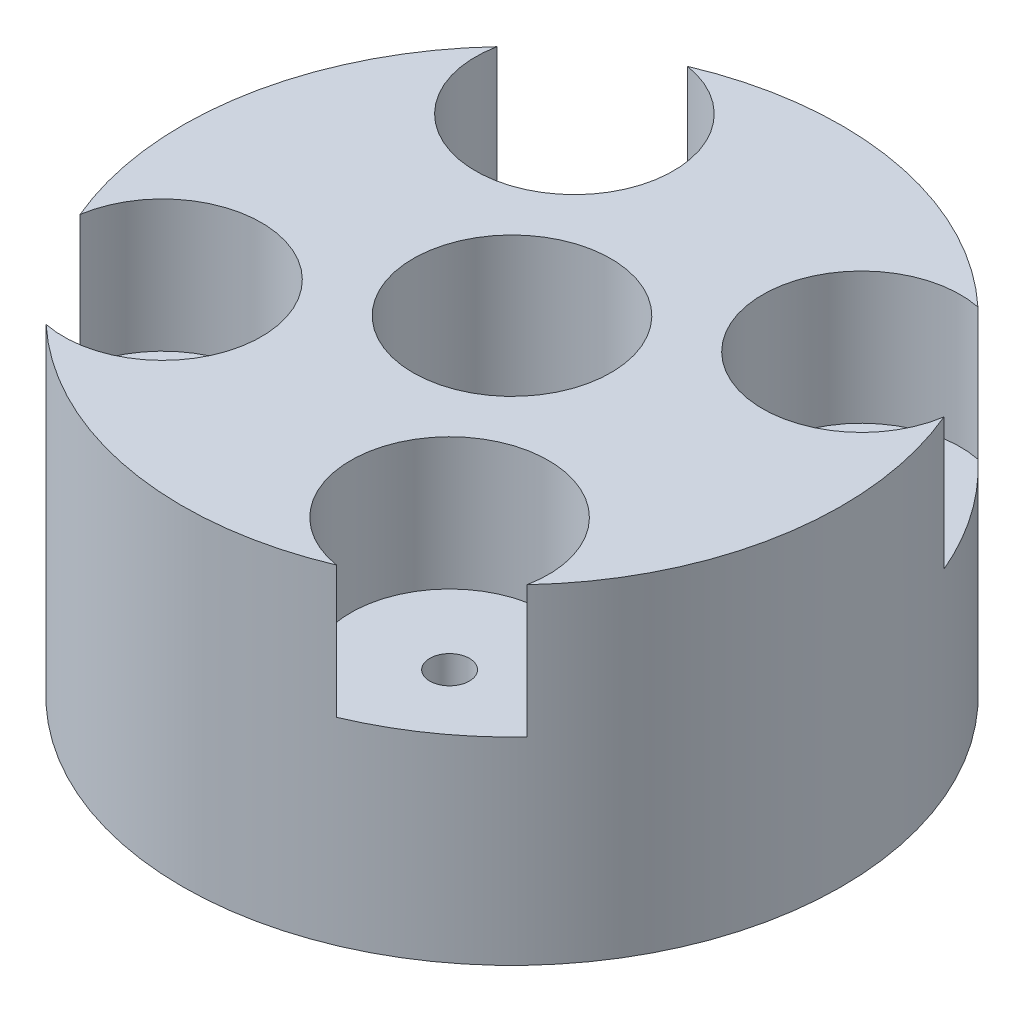
SolidWorks part; units mm, degrees
ref_plane "Alzado" through (0, 0, 0) normal (0, 0, 1) x (1, 0, 0)
ref_plane "Planta" through (0, 0, 0) normal (0, 1, 0) x (1, 0, 0)
ref_plane "Vista lateral" through (0, 0, 0) normal (1, 0, 0) x (0, 0, -1)
sketch "Croquis1" plane through (0, 0, 0) normal (0, 1, 0) x (1, 0, 0)
  circle A0 centre (0, 0) radius 10
  dimension "D1" = 20
extrude "Saliente-Extruir1" add sketch "Croquis1" along normal blind 10
sketch "Croquis2" plane through (0, 0, 0) normal (0, -1, 0) x (1, 0, 0)
  line L1 (5, 0) -> (2.5, 4.3301)
  line L2 (2.5, 4.3301) -> (-2.5, 4.3301)
  line L3 (-2.5, 4.3301) -> (-5, 0)
  line L4 (-5, 0) -> (-2.5, -4.3301)
  line L5 (-2.5, -4.3301) -> (2.5, -4.3301)
  line L6 (2.5, -4.3301) -> (5, 0)
  circle A0 centre (0, 0) radius 4.3301 construction
  dimension "D1" = 5
extrude "Cortar-Extruir1" cut sketch "Croquis2" against normal blind 5
sketch "Croquis3" plane through (0, 0, 0) normal (0, -1, 0) x (1, 0, 0)
  circle A0 centre (-6.248, 4.3547) radius 0.6
  circle A1 centre (6.248, -4.3547) radius 0.6
  circle A2 centre (4.3547, 6.248) radius 0.6
  circle A3 centre (-4.3547, -6.248) radius 0.6
  dimension "D1" = 1.2
extrude "Cortar-Extruir2" cut sketch "Croquis3" against normal blind 10
sketch "Croquis4" plane through (0, 10, 0) normal (0, 1, 0) x (1, 0, 0)
  circle A0 centre (0, 0) radius 3
  dimension "D1" = 6
extrude "Cortar-Extruir3" cut sketch "Croquis4" against normal blind 5
sketch "Croquis5" plane through (0, 10, 0) normal (0, 1, 0) x (1, 0, 0)
  circle A0 centre (6.248, 4.3547) radius 3
  circle A1 centre (-4.3547, 6.248) radius 3
  circle A2 centre (-6.248, -4.3547) radius 3
  circle A3 centre (4.3547, -6.248) radius 3
  dimension "D1" = 6
extrude "Cortar-Extruir4" cut sketch "Croquis5" against normal blind 4
